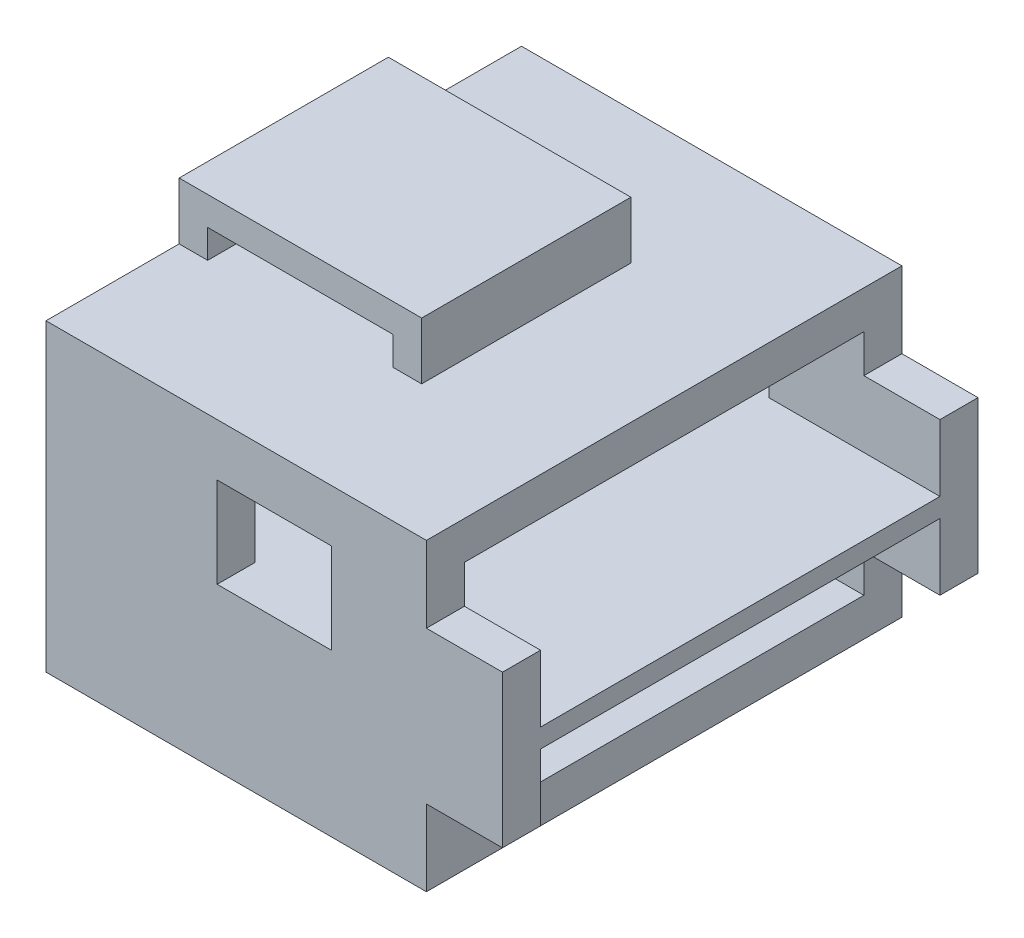
SolidWorks part; units mm, degrees
ref_plane "Front Plane" through (0, 0, 0) normal (0, 0, 1) x (1, 0, 0)
ref_plane "Top Plane" through (0, 0, 0) normal (0, 1, 0) x (1, 0, 0)
ref_plane "Right Plane" through (0, 0, 0) normal (1, 0, 0) x (0, 0, -1)
sketch "Croquis1" plane through (0, 0, 0) normal (0, 1, 0) x (1, 0, 0)
  line L1 (-10, 12.5) -> (10, 12.5)
  line L2 (-10, 12.5) -> (-10, -12.5)
  line L3 (-10, -12.5) -> (10, -12.5)
  line L4 (10, 12.5) -> (10, -12.5)
  line L5 (-10, 12.5) -> (10, -12.5) construction
  line L6 (-10, -12.5) -> (10, 12.5) construction
  point P0 (0, 0)
  dimension "D1" = 20
  dimension "D2" = 25
extrude "Saliente-Extruir4" add sketch "Croquis1" along normal blind 16
sketch "Croquis4" plane through (0, 0, 0) normal (1, 0, 0) x (0, 0, -1)
  line L0 (-12.5, 16) -> (12.5, 16) construction
  line L1 (-10.5, 14) -> (10.5, 14)
  line L2 (-10.5, 14) -> (-10.5, 2)
  line L3 (-10.5, 2) -> (10.5, 2)
  line L4 (10.5, 14) -> (10.5, 2)
  line L5 (-10.5, 14) -> (10.5, 2) construction
  line L6 (-10.5, 2) -> (10.5, 14) construction
  line L7 (-12.5, 16) -> (-12.5, 0) construction
  line L8 (-12.5, 0) -> (12.5, 0) construction
  line L9 (12.5, 16) -> (12.5, 0) construction
  point P0 (0, 8)
  dimension "D1" = 2
  dimension "D2" = 2
  dimension "D3" = 2
  dimension "D4" = 2
extrude "Cortar-Extruir1" cut sketch "Croquis4" against normal blind 18 from surface at 10 starting at face at (10, 8, 0)
sketch "Croquis5" plane through (0, 0, 0) normal (1, 0, 0) x (0, 0, -1)
  line L0 (10.5, 14) -> (-10.5, 14) construction
  line L2 (10.5, 2) -> (10.5, 14) construction
  line L3 (-10.5, 8.5) -> (10.5, 8.5)
  line L4 (-10.5, 8.5) -> (-10.5, 7.5)
  line L5 (-10.5, 7.5) -> (10.5, 7.5)
  line L6 (10.5, 8.5) -> (10.5, 7.5)
  line L7 (-10.5, 8.5) -> (10.5, 7.5) construction
  line L8 (-10.5, 7.5) -> (10.5, 8.5) construction
  point P4 (0, 8)
  dimension "D1" = 1
  dimension "D2" = 21
  dimension "D3" = 0
  dimension "D4" = 5.5
extrude "Saliente-Extruir6" add sketch "Croquis5" along normal blind 24 from surface at -10 starting at face at (-10, 8, 0)
sketch "Croquis7" plane through (0, 0, 0) normal (1, 0, 0) x (0, 0, -1)
  line L0 (-12.5, 16) -> (-12.5, 0) construction
  line L1 (-12.5, 12) -> (-10.5, 12)
  line L2 (-12.5, 12) -> (-12.5, 4)
  line L3 (-12.5, 4) -> (-10.5, 4)
  line L4 (-10.5, 12) -> (-10.5, 4)
  line L5 (-12.5, 12) -> (-10.5, 4) construction
  line L6 (-12.5, 4) -> (-10.5, 12) construction
  line L7 (-10.5, 7.5) -> (-10.5, 2) construction
  line L9 (-12.5, 16) -> (12.5, 16) construction
  line L10 (-12.5, 0) -> (12.5, 0) construction
  line L11 (0, 8) -> (0, 5.1009) construction
  line L12 (12.5, 12) -> (12.5, 4)
  line L13 (12.5, 4) -> (10.5, 4)
  line L14 (10.5, 12) -> (10.5, 4)
  line L15 (12.5, 4) -> (10.5, 12) construction
  line L16 (12.5, 12) -> (10.5, 4) construction
  line L17 (12.5, 12) -> (10.5, 12)
  point P0 (-11.5, 8)
  dimension "D1" = 0
  dimension "D2" = 0
  dimension "D3" = 4
  dimension "D4" = 4
extrude "Saliente-Extruir7" add sketch "Croquis7" along normal blind 4 from surface at 10 starting at face at (10, 8, 0)
sketch "Croquis8" plane through (0, 0, 0) normal (0, 1, 0) x (1, 0, 0)
  line L0 (-10, 12.5) -> (-10, -12.5) construction
  line L1 (-10, 5.5) -> (2.75, 5.5)
  line L2 (-10, 5.5) -> (-10, -5.5)
  line L3 (-10, -5.5) -> (2.75, -5.5)
  line L4 (2.75, 5.5) -> (2.75, -5.5)
  line L5 (-10, 5.5) -> (2.75, -5.5) construction
  line L6 (-10, -5.5) -> (2.75, 5.5) construction
  line L9 (10, 12.5) -> (-10, 12.5) construction
  point P0 (-3.625, 0)
  point P7 (-3.625, 0)
  dimension "D1" = 0
  dimension "D2" = 12.75
  dimension "D3" = 11
  dimension "D4" = 7
extrude "Saliente-Extruir8" add sketch "Croquis8" along normal blind 3 from surface at 16 starting at face at (0, 16, 0)
sketch "Croquis9" plane through (0, 0, 0) normal (0, 0, 1) x (1, 0, 0)
  line L0 (2.75, 16) -> (-10, 16) construction
  line L1 (-8.5, 17.5) -> (1.25, 17.5)
  line L2 (-8.5, 17.5) -> (-8.5, 16)
  line L3 (-8.5, 16) -> (1.25, 16)
  line L4 (1.25, 17.5) -> (1.25, 16)
  line L5 (-8.5, 17.5) -> (1.25, 16) construction
  line L6 (-8.5, 16) -> (1.25, 17.5) construction
  line L7 (2.75, 19) -> (-10, 19) construction
  line L8 (-10, 19) -> (-10, 16) construction
  line L9 (2.75, 19) -> (2.75, 16) construction
  point P0 (-3.625, 16.75)
  dimension "D1" = 0
  dimension "D2" = 1.5
  dimension "D3" = 1.5
  dimension "D4" = 1.5
extrude "Cortar-Extruir2" cut sketch "Croquis9" against normal mid plane 23
sketch "Croquis11" plane through (0, 0, 0) normal (0, 0, 1) x (1, 0, 0)
  line L1 (-1, 13.25) -> (5, 13.25)
  line L2 (-1, 13.25) -> (-1, 8.5)
  line L3 (-1, 8.5) -> (5, 8.5)
  line L4 (5, 13.25) -> (5, 8.5)
  line L5 (-1, 13.25) -> (5, 8.5) construction
  line L6 (-1, 8.5) -> (5, 13.25) construction
  line L7 (-10, 16) -> (-10, 0) construction
  line L12 (14, 8.5) -> (-8, 8.5) construction
  point P0 (2, 10.875)
  dimension "D1" = 4.75
  dimension "D2" = 0
  dimension "D3" = 6
  dimension "D4" = 9
extrude "Cortar-Extruir4" cut sketch "Croquis11" against normal mid plane 33
sketch "Croquis12" plane through (0, 0, 0) normal (1, 0, 0) x (0, 0, -1)
  line L1 (3, 6.75) -> (-3, 6.75)
  line L2 (3, 6.75) -> (3, 2)
  line L3 (3, 2) -> (-3, 2)
  line L4 (-3, 6.75) -> (-3, 2)
  line L5 (3, 6.75) -> (-3, 2) construction
  line L6 (3, 2) -> (-3, 6.75) construction
  line L7 (-10.5, 2) -> (10.5, 2) construction
  line L8 (-10.5, 7.5) -> (-10.5, 2) construction
  point P0 (0, 4.375)
  point P5 (0, 4.25)
  dimension "D1" = 0
  dimension "D2" = 6
  dimension "D3" = 4.75
  dimension "D5" = 7.5
extrude "Cortar-Extruir5" cut sketch "Croquis12" against normal blind 33
